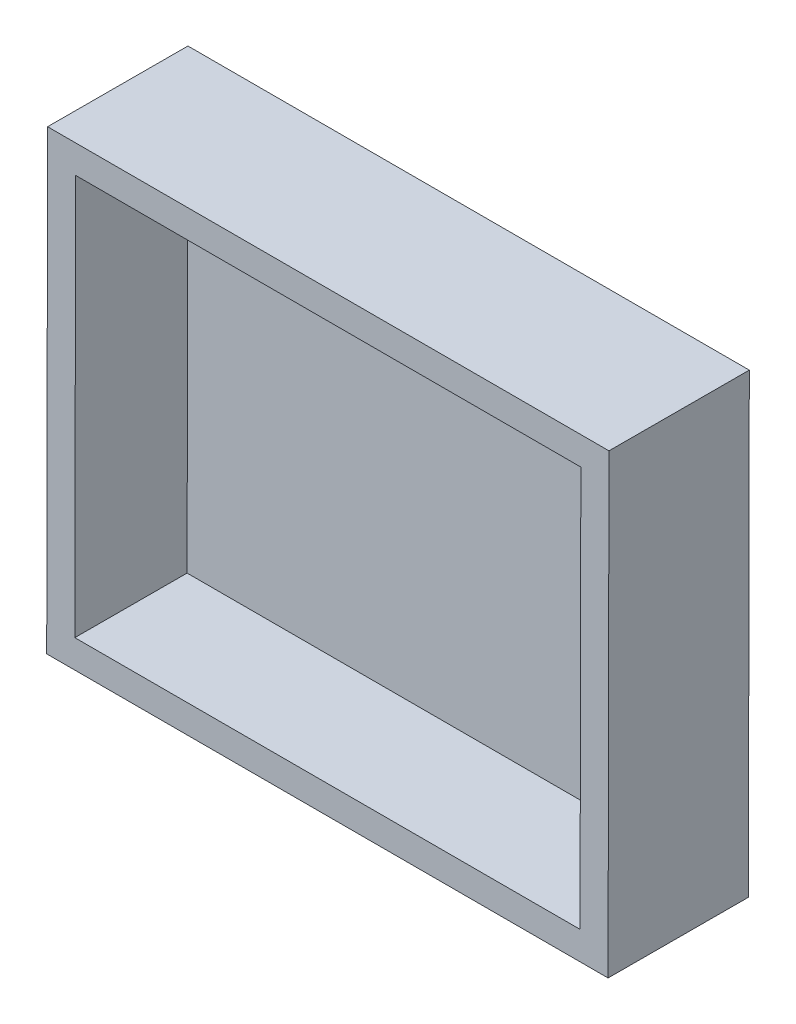
SolidWorks part; units mm, degrees
ref_plane "Front Plane" through (0, 0, 0) normal (0, 0, 1) x (1, 0, 0)
ref_plane "Top Plane" through (0, 0, 0) normal (0, 1, 0) x (1, 0, 0)
ref_plane "Right Plane" through (0, 0, 0) normal (1, 0, 0) x (0, 0, -1)
ref_plane "Plane1" through (0, -0.0001, -0.0526) normal (0, 0.002, 1) x (1, 0, 0)
sketch "Sketch2" plane through (0, -0.0001, -0.0526) normal (0, 0.002, 1) x (1, 0, 0)
  line L0 (-75.064, -32.8936) -> (-67.505, -32.8936)
  line L2 (-2.496, 32.1063) -> (-62.496, 32.1063)
  line L11 (4.936, 32.1063) -> (4.936, -32.8936)
  line L12 (-75.064, 32.1063) -> (-75.064, -32.8936)
  line L16 (4.936, -32.8936) -> (-67.505, -32.8936)
  line L26 (4.936, 32.1063) -> (-2.496, 32.1063)
  line L34 (-62.496, 32.1063) -> (-75.064, 32.1063)
  dimension "D1" = 7.559
  dimension "D2" = 60
  dimension "D3" = 64.9999
  dimension "D4" = 72.441
  dimension "D6" = 7.432
  dimension "D9" = 12.568
extrude "Boss-Extrude1" add sketch "Sketch2" along normal blind 20
shell "Shell2" thickness 4
